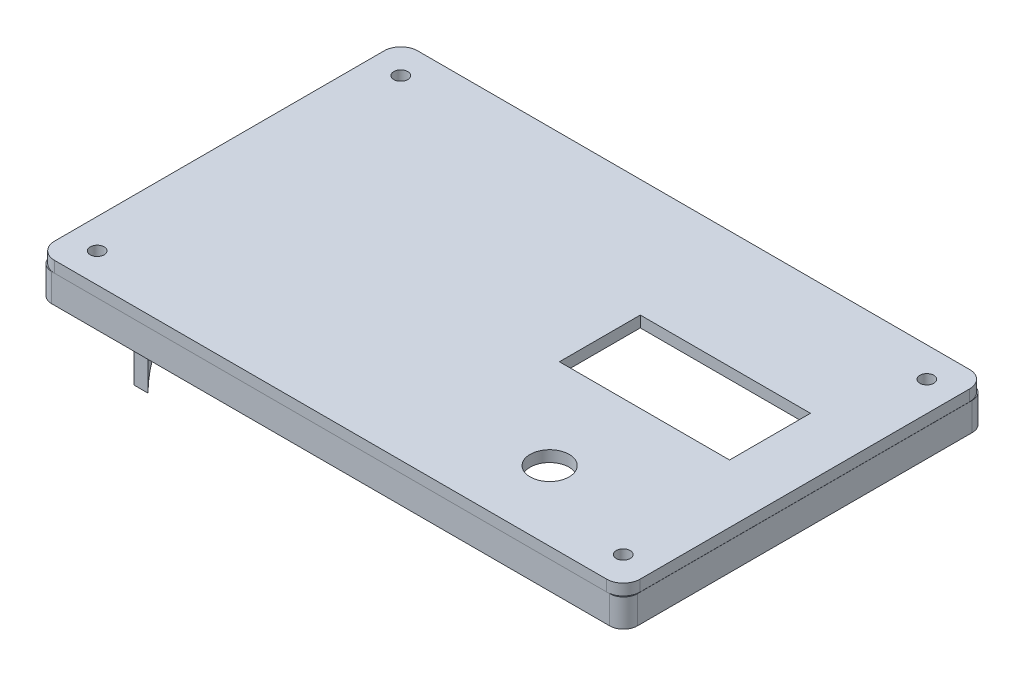
SolidWorks part; units mm, degrees
ref_plane "Спереди" through (0, 0, 0) normal (0, 0, 1) x (1, 0, 0)
ref_plane "Сверху" through (0, 0, 0) normal (0, 1, 0) x (1, 0, 0)
ref_plane "Справа" through (0, 0, 0) normal (1, 0, 0) x (0, 0, -1)
sketch "Эскиз1" plane through (0, 0, 0) normal (0, 1, 0) x (1, 0, 0)
  line L0 (-34.5539, 0) -> (36.3395, 0) construction
  line L1 (-40.9449, 30) -> (40.9449, 30)
  line L2 (-50, 21.0165) -> (-50, -21.0165)
  line L3 (-40.9449, -30) -> (40.9449, -30)
  line L4 (50, 21.0165) -> (50, -21.0165)
  line L5 (-50, 32.5) -> (50, 32.5)
  line L6 (-52.5, -27.5) -> (-52.5, -30)
  line L7 (-50, -32.5) -> (50, -32.5)
  line L8 (52.5, 30) -> (52.5, -30)
  line L12 (-52.5, 27.5) -> (-52.5, -27.5)
  line L13 (-52.5, 27.5) -> (-52.5, 30)
  arc A0 (50, 32.5) -> (52.5, 30) centre (50, 30) cw
  arc A1 (52.5, -30) -> (50, -32.5) centre (50, -30) cw
  arc A2 (-50, -32.5) -> (-52.5, -30) centre (-50, -30) cw
  arc A3 (-50, 32.5) -> (-52.5, 30) centre (-50, 30) ccw
  arc A4 (-42.9287, 27.7464) -> (-40.9449, 30) centre (-40.9449, 28) cw
  arc A12 (-47.7262, 22.9977) -> (-42.9287, 27.7464) centre (-47.1445, 27.2076) ccw
  circle A13 centre (-47.1445, 27.2076) radius 1.25
  arc A14 (-47.7262, 22.9977) -> (-50, 21.0165) centre (-48, 21.0165) ccw
  arc A15 (47.7262, -22.9977) -> (50, -21.0165) centre (48, -21.0165) ccw
  arc A16 (47.7262, -22.9977) -> (42.9287, -27.7464) centre (47.1445, -27.2076) ccw
  circle A17 centre (47.1445, -27.2076) radius 1.25
  arc A18 (42.9287, -27.7464) -> (40.9449, -30) centre (40.9449, -28) cw
  circle A19 centre (47.1445, 27.2076) radius 1.25
  arc A20 (47.7262, 22.9977) -> (50, 21.0165) centre (48, 21.0165) cw
  arc A21 (47.7262, 22.9977) -> (42.9287, 27.7464) centre (47.1445, 27.2076) cw
  arc A22 (42.9287, 27.7464) -> (40.9449, 30) centre (40.9449, 28) ccw
  arc A23 (-42.9287, -27.7464) -> (-40.9449, -30) centre (-40.9449, -28) ccw
  circle A24 centre (-47.1445, -27.2076) radius 1.25
  arc A25 (-47.7262, -22.9977) -> (-42.9287, -27.7464) centre (-47.1445, -27.2076) cw
  arc A26 (-47.7262, -22.9977) -> (-50, -21.0165) centre (-48, -21.0165) cw
  point P24 (-50, 30)
  point P27 (50, 30)
  point P32 (-50, -30)
  point P35 (-82.5, -30)
  point P38 (-52.5, -30)
  point P60 (0, 0)
  dimension "D11" = 2.5
  dimension "D12" = 2.5
  dimension "D13" = 3
  dimension "D14" = 2
  dimension "D15" = 2
  dimension "D2" = 2.5
  dimension "D5" = 2.5
  dimension "D1" = 100
  dimension "D3" = 2.5
  dimension "D4" = 2.5
  dimension "D6" = 2.5
  dimension "D8" = 2.5
  dimension "D9" = 30
  dimension "D16" = 50
  dimension "D17" = 30
  dimension "D18" = 2
extrude "Бобышка-Вытянуть1" add sketch "Эскиз1" along normal blind 5
sketch "Эскиз2" plane through (0, 0, 0) normal (0, -1, 0) x (1, 0, 0)
  line L0 (-52.5, -30) -> (-52.5, 30) construction
  line L1 (-52.5, -15.25) -> (-50, -15.25)
  line L2 (-52.5, -15.25) -> (-52.5, 15.25)
  line L3 (-52.5, 15.25) -> (-50, 15.25)
  line L4 (-50, -15.25) -> (-50, 15.25)
  line L5 (-50, -21.0165) -> (-50, 21.0165) construction
  line L6 (50, -32.5) -> (-50, -32.5) construction
  dimension "D1" = 17.25
  dimension "D2" = 30.5
extrude "Бобышка-Вытянуть2" add sketch "Эскиз2" along normal blind 22.5
sketch "Эскиз3" plane through (-52.5, 0, 0) normal (-1, 0, 0) x (0, 0, 1)
  line L0 (15.25, -22.5) -> (-15.25, -22.5) construction
  line L1 (-15.25, -22.5) -> (15.25, -22.5)
  arc A0 (-15.25, -22.5) -> (15.25, -22.5) centre (0, -22.5) cw
extrude "Вырез-Вытянуть1" cut sketch "Эскиз3" against normal up to next
sketch "Эскиз4" plane through (0, 5, 0) normal (0, 1, 0) x (1, 0, 0)
  line L0 (-40.9449, -30) -> (40.9449, -30) construction
  line L1 (-49.4757, 32.5629) -> (49.4757, 32.5629)
  line L2 (-52.4757, 29.5629) -> (-52.4757, -29.5091)
  line L3 (-49.4757, -32.5091) -> (49.4757, -32.5091)
  line L4 (52.4757, 29.5629) -> (52.4757, -29.5091)
  line L5 (50, -21.0165) -> (50, 21.0165) construction
  line L6 (11.5, 11.5) -> (42, 11.5)
  line L7 (11.5, 11.5) -> (11.5, -3)
  line L8 (11.5, -3) -> (42, -3)
  line L9 (42, 11.5) -> (42, -3)
  line L10 (26.75, 11.5) -> (26.75, -26.2674) construction
  arc A0 (49.4757, -32.5091) -> (52.4757, -29.5091) centre (49.4757, -29.5091) ccw
  arc A1 (52.4757, 29.5629) -> (49.4757, 32.5629) centre (49.4757, 29.5629) ccw
  arc A2 (-49.4757, 32.5629) -> (-52.4757, 29.5629) centre (-49.4757, 29.5629) ccw
  arc A3 (-52.4757, -29.5091) -> (-49.4757, -32.5091) centre (-49.4757, -29.5091) ccw
  circle A4 centre (26.75, -20) radius 3.5
  circle A5 centre (-47.1445, 27.2076) radius 1.25
  circle A6 centre (47.1445, 27.2076) radius 1.25
  circle A7 centre (47.1445, -27.2076) radius 1.25
  circle A8 centre (-47.1445, -27.2076) radius 1.25
  dimension "D1" = 3
  dimension "D2" = 10
  dimension "D3" = 14.5
  dimension "D4" = 30.5
  dimension "D5" = 8
  dimension "D6" = 17
extrude "Бобышка-Вытянуть3" add sketch "Эскиз4" along normal blind 2
